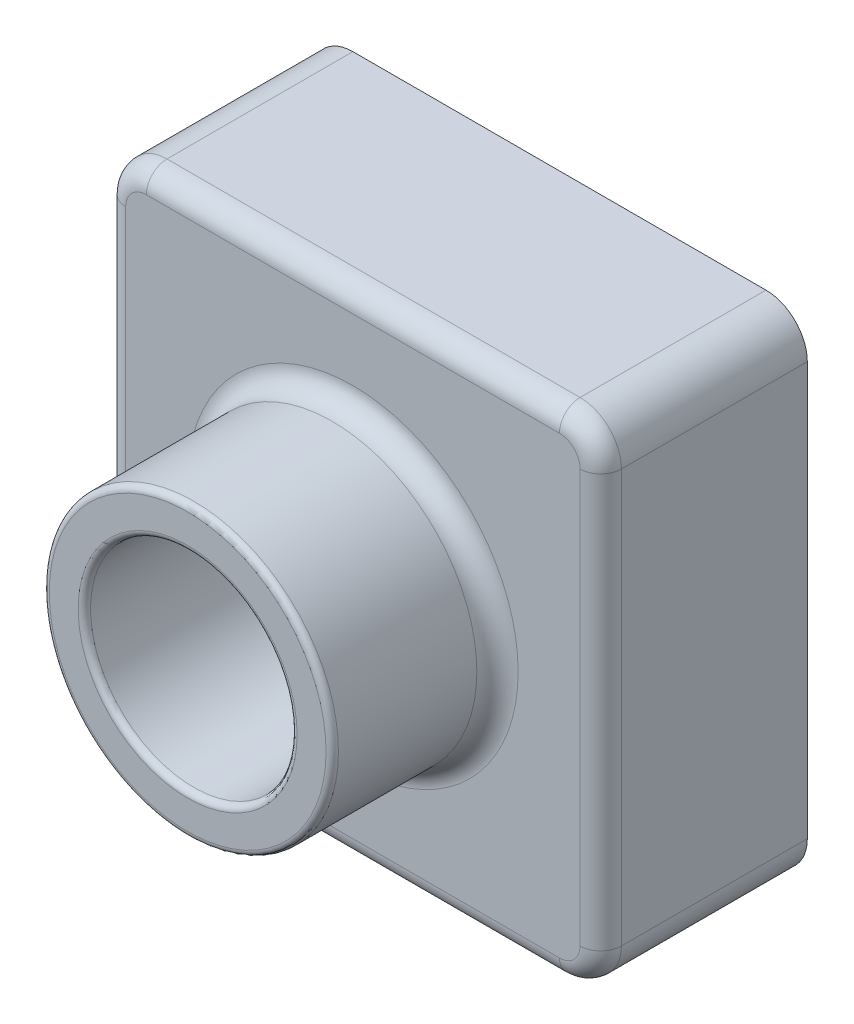
SolidWorks part; units mm, degrees
material "Chrome Stainless Steel"
ref_plane "Front Plane" through (0, 0, 0) normal (0, 0, 1) x (1, 0, 0)
ref_plane "Top Plane" through (0, 0, 0) normal (0, 1, 0) x (1, 0, 0)
ref_plane "Right Plane" through (0, 0, 0) normal (1, 0, 0) x (0, 0, -1)
sketch "Sketch1" plane through (0, 0, 0) normal (0, 0, 1) x (1, 0, 0)
  line L1 (-55.3709, 28.4866) -> (64.6291, 28.4866)
  line L2 (-55.3709, 28.4866) -> (-55.3709, -91.5134)
  line L3 (-55.3709, -91.5134) -> (64.6291, -91.5134)
  line L4 (64.6291, 28.4866) -> (64.6291, -91.5134)
  dimension "D1" = 120
  dimension "D2" = 120
extrude "Boss-Extrude1" add sketch "Sketch1" along normal blind 50
sketch "Sketch2" plane through (0, 0, 50) normal (0, 0, 1) x (1, 0, 0)
  line L0 (64.6291, 28.4866) -> (-55.3709, 28.4866) construction
  line L3 (64.6291, -91.5134) -> (64.6291, 28.4866) construction
  circle A0 centre (4.6291, -31.5134) radius 35
  dimension "D1" = 70
  dimension "D2" = 60
  dimension "D3" = 60
extrude "Boss-Extrude2" add sketch "Sketch2" along normal blind 40
sketch "Sketch3" plane through (0, 0, 90) normal (0, 0, 1) x (1, 0, 0)
  circle A0 centre (4.6291, -31.5134) radius 25
  dimension "D1" = 50
extrude "Cut-Extrude1" cut sketch "Sketch3" against normal through all
fillet "Fillet2" radius 10 4 edges at (-55.3709, -91.5134, 25) (64.6291, -91.5134, 25) (-55.3709, 28.4866, 25) (64.6291, 28.4866, 25)
fillet "Fillet3" radius 1.5 2 edges at (39.6291, -31.5134, 90) (29.6291, -31.5134, 90)
fillet "Fillet4" radius 5 9 edges at (-52.442, 25.5577, 50) (4.6291, 28.4866, 50) (61.7001, 25.5577, 50) (64.6291, -31.5134, 50) (61.7001, -88.5844, 50) (4.6291, -91.5134, 50) (-52.442, -88.5844, 50) (-55.3709, -31.5134, 50) (39.6291, -31.5134, 50)
shell "Shell1" thickness 2
